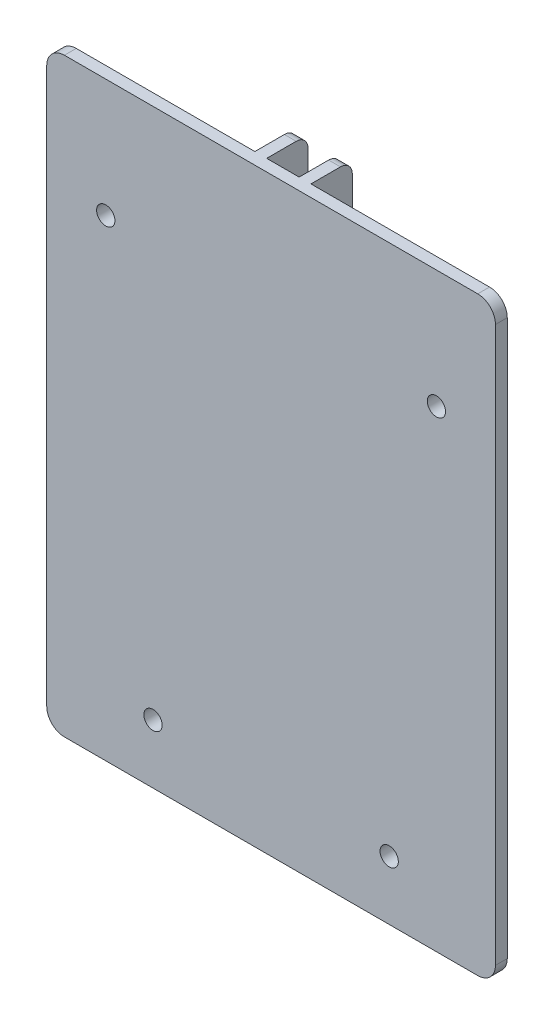
SolidWorks part; units mm, degrees
ref_plane "Plan de face" through (0, 0, 0) normal (0, 0, 1) x (1, 0, 0)
ref_plane "Plan de dessus" through (0, 0, 0) normal (0, 1, 0) x (1, 0, 0)
ref_plane "Plan de droite" through (0, 0, 0) normal (1, 0, 0) x (0, 0, -1)
sketch "Esquisse1" plane through (0, 0, 0) normal (0, 0, 1) x (1, 0, 0)
  line L1 (0, 0) -> (76, 0)
  line L2 (0, 0) -> (0, 100)
  line L3 (0, 100) -> (76, 100)
  line L4 (76, 0) -> (76, 100)
extrude "Boss.-Extru.1" add sketch "Esquisse1" along normal blind 9
sketch "Esquisse2" plane through (0, 0, 0) normal (0, 0, -1) x (-1, 0, 0)
  line L1 (-33.25, 100) -> (0, 100)
  line L2 (-33.25, 100) -> (-33.25, 0)
  line L3 (-33.25, 0) -> (0, 0)
  line L4 (0, 100) -> (0, 0)
  line L5 (-76, 100) -> (-42.75, 100)
  line L6 (-76, 100) -> (-76, 0)
  line L7 (-76, 0) -> (-42.75, 0)
  line L8 (-42.75, 100) -> (-42.75, 0)
  line L9 (-35.25, 100) -> (-40.75, 100)
  line L10 (-35.25, 100) -> (-35.25, 0)
  line L11 (-35.25, 0) -> (-40.75, 0)
  line L12 (-40.75, 100) -> (-40.75, 0)
extrude "Enlèv. mat.-Extru.1" cut sketch "Esquisse2" against normal blind 7
sketch "Esquisse3" plane through (42.75, 0, 0) normal (1, 0, 0) x (0, 0, -1)
  circle A0 centre (-3.5, 20) radius 1.55
  circle A1 centre (-3.5, 90) radius 1.55
  point P2 (0, 0)
  point P5 (0, 0)
  point P6 (0, 0)
extrude "Enlèv. mat.-Extru.2" cut sketch "Esquisse3" against normal through all
fillet "Congé1" radius 3 4 edges at (0, 0, 8) (76, 0, 8) (0, 100, 8) (76, 100, 8)
fillet "Congé2" radius 2 4 edges at (34.25, 0, 0) (41.75, 0, 0) (34.25, 100, 0) (41.75, 100, 0)
sketch "Esquisse9" plane through (0, 0, 7) normal (0, 0, -1) x (-1, 0, 0)
  circle A1 centre (-66, 80) radius 3
  circle A2 centre (-10, 80) radius 3
  circle A3 centre (-18, 10) radius 3
  circle A4 centre (-58, 10) radius 3
  point P8 (0, 0)
  point P9 (0, 0)
  point P10 (0, 0)
  point P11 (0, 0)
extrude "Boss.-Extru.2" add sketch "Esquisse9" along normal blind 3
sketch "Esquisse5" plane through (0, 0, 7) normal (0, 0, -1) x (-1, 0, 0)
  circle A0 centre (-66, 80) radius 1.55
  circle A1 centre (-58, 10) radius 1.55
  circle A2 centre (-18, 10) radius 1.55
  circle A3 centre (-10, 80) radius 1.55
  point P8 (0, 0)
  point P9 (0, 0)
  point P10 (0, 0)
  point P11 (0, 0)
extrude "Enlèv. mat.-Extru.4" cut sketch "Esquisse5" against normal through all both and the other way through all
